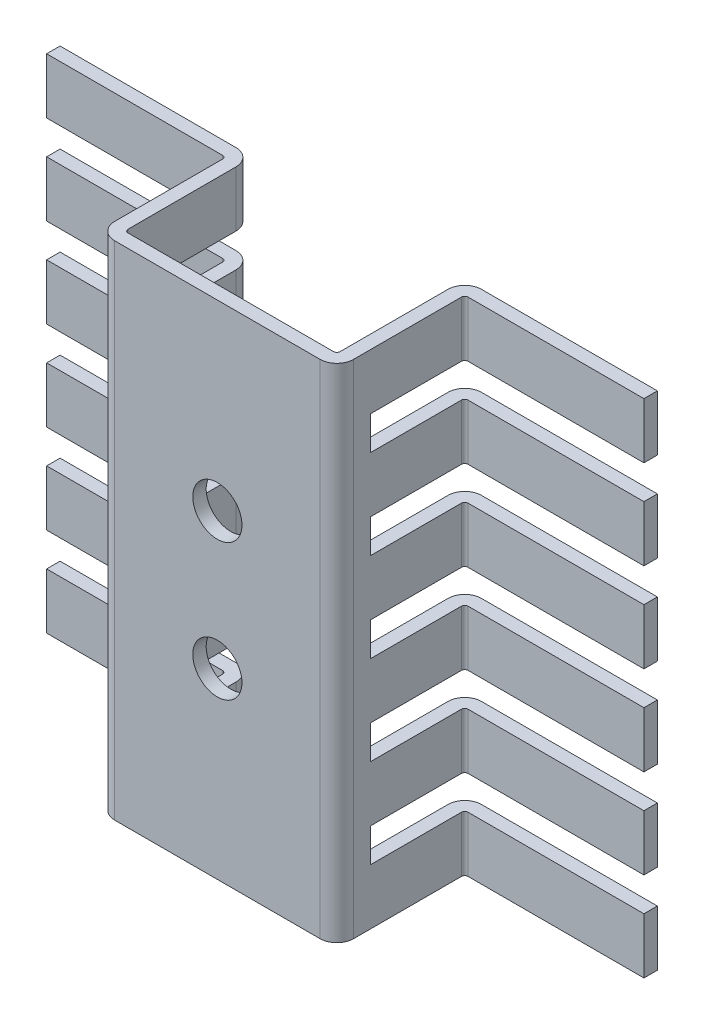
SolidWorks part; units mm, degrees
ref_plane "Front" through (0, 0, 0) normal (0, 0, 1) x (1, 0, 0)
ref_plane "Top" through (0, 0, 0) normal (0, 1, 0) x (1, 0, 0)
ref_plane "Right" through (0, 0, 0) normal (1, 0, 0) x (0, 0, -1)
sketch "Sketch1" plane through (0, 0, 0) normal (0, 1, 0) x (1, 0, 0)
  line L0 (-8.89, 0) -> (8.89, 0)
  line L1 (8.89, 0) -> (8.89, 9.52)
  line L2 (8.89, 9.52) -> (22.225, 9.52)
  line L3 (-8.89, 0) -> (-8.89, 9.52)
  line L4 (-8.89, 9.52) -> (-22.225, 9.52)
  dimension "D1" = 17.78
  dimension "D2" = 44.45
  dimension "D3" = 9.52
extrude "Extrude-Thin1" add sketch "Sketch1" along normal blind 37.34 thin thin type one direction wall 1
sketch "Sketch2" plane through (0, 0, 0) normal (0, 0, 1) x (1, 0, 0)
  line L0 (0, -1.2906) -> (0, 38.2454) construction
  line L1 (7.64, 0) -> (-7.64, 0) construction
  circle A0 centre (0, 13.59) radius 1.83
  circle A1 centre (0, 23.75) radius 1.83
  dimension "D1" = 3.66
  dimension "D3" = 3.66
  dimension "D2" = 13.59
  dimension "D4" = 10.16
extrude "Cut-Extrude1" cut sketch "Sketch2" against normal through all
sketch "Sketch3" plane through (0, 0, -10.52) normal (0, 0, -1) x (-1, 0, 0)
  line L0 (-22.225, 37.34) -> (-22.225, 0) construction
  line L1 (-22.225, 33.2) -> (22.225, 33.2)
  line L2 (-22.225, 33.2) -> (-22.225, 30.7)
  line L3 (-22.225, 30.7) -> (22.225, 30.7)
  line L4 (22.225, 33.2) -> (22.225, 30.7)
  line L5 (22.225, 37.34) -> (22.225, 0) construction
  line L6 (-22.225, 37.34) -> (-22.225, 33.2) construction
  line L7 (-22.225, 26.56) -> (22.225, 26.56)
  line L8 (-22.225, 26.56) -> (-22.225, 24.06)
  line L9 (-22.225, 24.06) -> (22.225, 24.06)
  line L10 (22.225, 26.56) -> (22.225, 24.06)
  line L11 (-22.225, 19.92) -> (22.225, 19.92)
  line L12 (-22.225, 19.92) -> (-22.225, 17.42)
  line L13 (-22.225, 17.42) -> (22.225, 17.42)
  line L14 (22.225, 19.92) -> (22.225, 17.42)
  line L15 (-22.225, 13.28) -> (22.225, 13.28)
  line L16 (-22.225, 13.28) -> (-22.225, 10.78)
  line L17 (-22.225, 10.78) -> (22.225, 10.78)
  line L18 (22.225, 13.28) -> (22.225, 10.78)
  line L19 (-22.225, 6.64) -> (22.225, 6.64)
  line L20 (-22.225, 6.64) -> (-22.225, 4.14)
  line L21 (-22.225, 4.14) -> (22.225, 4.14)
  line L22 (22.225, 6.64) -> (22.225, 4.14)
  line L23 (-22.225, 30.7) -> (-22.225, 26.56) construction
  line L24 (-22.225, 24.06) -> (-22.225, 19.92) construction
  line L25 (-22.225, 17.42) -> (-22.225, 13.28) construction
  line L26 (-22.225, 10.78) -> (-22.225, 6.64) construction
  line L27 (-22.225, 4.14) -> (-22.225, 0) construction
  dimension "D1" = 2.5
extrude "Cut-Extrude2" cut sketch "Sketch3" against normal blind 8
